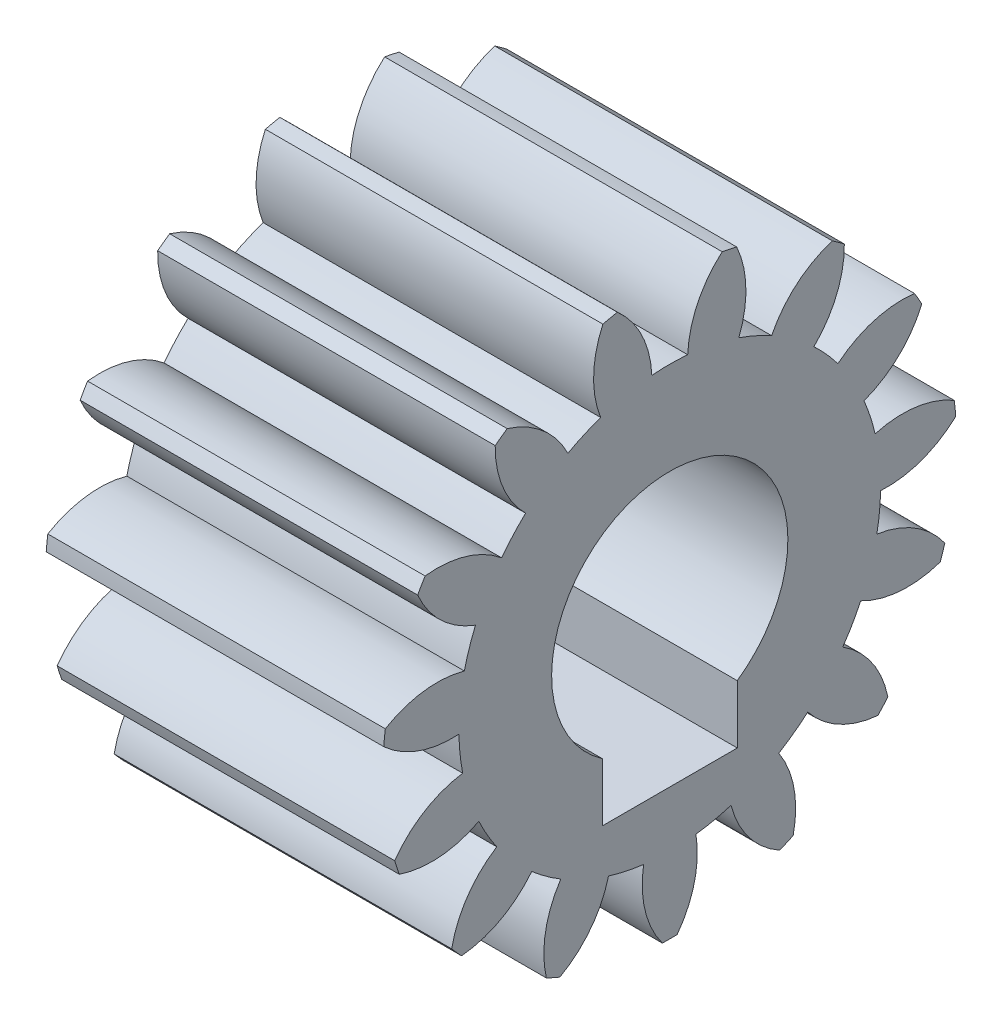
SolidWorks part; units mm, degrees
ref_plane "Plane1" through (0, 0, 0) normal (0, 0, 1) x (1, 0, 0)
ref_plane "Plane2" through (0, 0, 0) normal (0, 1, 0) x (1, 0, 0)
ref_plane "Plane3" through (0, 0, 0) normal (1, 0, 0) x (0, 0, -1)
sketch "HoldingSke" plane through (0, 0, 0) normal (0, 1, 0) x (1, 0, 0)
  line L0 (0, 0) -> (1.9319, -0.5176)
  line L1 (-15, 0) -> (100, 0) construction
  line L2 (0, 0) -> (-2.1039, 2.3779)
  line L3 (0, 0) -> (-11.863, 4.5341)
  line L4 (0, 0) -> (8.3417, 2.2352)
  line L5 (0, 0) -> (-46.8476, -17.4728)
  line L6 (0, 0) -> (-4.1448, -2.7965)
  line L7 (-2.1039, 2.3779) -> (8.6586, 51.2059)
  line L8 (-76.2, 54.61) -> (-76.1, 54.61)
  line L9 (-71.009, 38.7566) -> (-53.1078, 45.2721)
  line L10 (-76.2, 71.12) -> (104.1128, 71.12)
  line L11 (0, 0) -> (-5, 0)
  line L12 (-76.2, 101.6) -> (-76.181, 101.6)
  line L13 (24.9733, 27.94) -> (52.9518, 28.4284)
  line L14 (24.9733, 27.94) -> (24.9743, 27.94)
  line L15 (24.9733, 27.94) -> (100.4006, 29.5858)
  line L16 (-63.627, -0.5) -> (-12.827, -0.5)
  circle A0 centre (0, 0) radius 0.5
  circle A1 centre (0, 0) radius 3.124
  circle A2 centre (0, 0) radius 37.5
  circle A3 centre (0, 0) radius 0.5
  dimension "MHD" = 6.248
  dimension "Hub_dia" = 75
  dimension "Bore" = 1
  dimension "MBD" = 1
  dimension "Num_teeth" = 15
  dimension "Pitch" = 2
  dimension "Overall_len" = 50
  dimension "Show_teeth" = 15
  dimension "Thickness" = 5
  dimension "OAL" = 50.0001
  dimension "T_dim" = 0.1
  dimension "Ap" = 20
  dimension "H" = 19.05
  dimension "Pitch_radius" = 180.3128
  dimension "Width" = 5
  dimension "Backlash" = 0.019
  dimension "Addendum_fac" = 1
  dimension "Dedendum_fac" = 1.25
  dimension "Clearance_fac" = 0.25
  dimension "Dedendum_add" = 0.001
  dimension "Module" = 0.5
sketch "BasProSke" plane through (0, 0, 0) normal (0, 1, 0) x (1, 0, 0)
  line L0 (-10, 0) -> (60, 0) construction
  line L1 (0, 0) -> (0, 4.25)
  line L2 (0, 0) -> (5, 0)
  line L3 (5, 0) -> (5, 4.25)
  line L4 (5, 4.25) -> (0, 4.25)
  dimension "Thickness" = 5
  dimension "Diameter" = 8.5
revolve "Base-Revolve" add sketch "BasProSke" angle 360 about L0
sketch "TooCutSke" plane through (0, 0, 0) normal (1, 0, 0) x (0, 0, -1)
  line L1 (0, 0) -> (0, 107) construction
  line L2 (0, 0) -> (-0.4252, 3.7258) construction
  line L3 (0, 0) -> (-1.5522, 7.3025) construction
  line L4 (-0.4252, 3.7258) -> (-0.7761, 3.6512) construction
  arc A0 (0.2658, 3.1127) -> (-0.2658, 3.1127) centre (0, 0) ccw
  arc A1 (0.8008, 4.1997) -> (-0.8008, 4.1997) centre (0, 0) ccw
  circle A2 centre (0, 0) radius 3.75 construction
  circle A3 centre (0, 0) radius 3.5238 construction
  arc A4 (-0.2658, 3.1127) -> (-0.8008, 4.1997) centre (-1.7645, 3.0503) ccw
  arc A5 (0.8008, 4.1997) -> (0.2658, 3.1127) centre (1.7645, 3.0503) ccw
  dimension "Root_dia" = 6.248
  dimension "Overcut_dia" = 8.5508
  dimension "Pitch_dia" = 7.5
  dimension "Base_dia" = 7.0477
  dimension "Flank_rad" = 1.5
  dimension "Half_ang" = 12
  dimension "Half_CT" = 0.3587
extrude "ToothCut" cut sketch "TooCutSke" along normal through all
fillet "Breaks" [suppressed] radius 0.01
fillet "RootFillets" [suppressed] radius 0.126
pattern_circular "TeethCuts" count 15 every 24 about axis through (-10, 0, 0) along (1, 0, 0) of "ToothCut", "RootFillets", "Breaks"
sketch "HubNeaOneSke" plane through (0, 0, 0) normal (-1, 0, 0) x (0, 0, 1)
  circle A0 centre (0, 0) radius 3.124
  dimension "Diameter" = 6.248
extrude "HubNearOne" [suppressed] add sketch "HubNeaOneSke" along normal blind 45.0001
sketch "HubNeaBotSke" plane through (0, 0, 0) normal (-1, 0, 0) x (0, 0, 1)
  circle A0 centre (0, 0) radius 3.124
  dimension "Diameter" = 6.248
extrude "HubNearBoth" [suppressed] add sketch "HubNeaBotSke" along normal blind 22.5
ref_plane "FarPln" through (5, 0, 0) normal (1, 0, 0) x (0, 0, -1)
sketch "HubFarSke" plane through (5, 0, 0) normal (1, 0, 0) x (0, 0, -1)
  circle A0 centre (0, 0) radius 3.124
  dimension "Diameter" = 6.248
extrude "HubFar" [suppressed] add sketch "HubFarSke" along normal blind 22.5
sketch "BorSke" plane through (0, 0, 0) normal (1, 0, 0) x (0, 0, -1)
  circle A0 centre (0, 0) radius 0.5
  dimension "Diameter" = 1
extrude "Bore" cut sketch "BorSke" along normal mid plane 100.0001
sketch "KeySke" plane through (0, 0, 0) normal (1, 0, 0) x (0, 0, -1)
  line L0 (-0.05, 0) -> (-0.05, 0.6)
  line L1 (-0.05, 0.6) -> (0.05, 0.6)
  line L2 (0.05, 0.6) -> (0.05, 0)
  line L3 (0, 0) -> (0, 34) construction
  line L4 (-0.05, 0) -> (0.05, 0)
  dimension "Offset" = 0.6
  dimension "Width" = 0.1
extrude "Keyway" [suppressed] cut sketch "KeySke" along normal mid plane 100.0001
pattern_circular "Keyway2" [suppressed] count 2 every 90 about axis through (-10, 0, 0) along (1, 0, 0)
sketch "Sketch1" plane through (5, 0, 0) normal (1, 0, 0) x (0, 0, -1)
  circle A0 centre (0, 0) radius 1.75
  dimension "D1" = 3.5
extrude "Cut-Extrude1" cut sketch "Sketch1" against normal through all both and the other way through all
sketch "Sketch2" plane through (5, 0, 0) normal (1, 0, 0) x (0, 0, -1)
  line L0 (0, 0) -> (0, -3.7965) construction
  line L1 (-1, -1.2) -> (1, -1.2)
  line L2 (-1, -1.2) -> (-1, -2.3)
  line L3 (-1, -2.3) -> (1, -2.3)
  line L4 (1, -1.2) -> (1, -2.3)
  line L5 (0, -2.3) -> (0, -1.2) construction
  line L6 (-1, -1.75) -> (1, -1.75) construction
  circle A0 centre (0, 0) radius 1.75 construction
  point P0 (0, -1.75)
  dimension "D1" = 2.3
  dimension "D2" = 2
extrude "Cut-Extrude2" cut sketch "Sketch2" against normal through all both and the other way through all
equation "' \"Module@HoldingSke\" = 6.35"
equation "' \"Num_teeth@HoldingSke\" = 12"
equation "' \"Ap@HoldingSke\" =  20"
equation "' \"Ap@HoldingSke\" = 20"
equation "' \"Width@HoldingSke\" = 0.5 * 25.4"
equation "' \"Hub_dia@HoldingSke\"= 1 * 25.4"
equation "' \"Hub_dia@HoldingSke\" = 1 * 25.4"
equation "' \"Overall_len@HoldingSke\" = 1.0 * 25.4"
equation "' \"Bore@HoldingSke\" = 0.75 * 25.4"
equation "' \"T_dim@HoldingSke\" = 0.1 * 25.4"
equation "' \"Width@KeySke\" = 0.25 * 25.4"
equation "' \"Show_teeth@HoldingSke\" = 13"
equation "' \"Backlash@HoldingSke\" = 0.009 * 25.4"
equation "' \"Addendum_fac@HoldingSke\" = 1.0"
equation "' \"Dedendum_fac@HoldingSke\" = 1.25"
equation "' \"Dedendum_add@HoldingSke\" = 0.00005 * 25.4"
equation "' \"Clearance_fac@HoldingSke\" = 0.25"
equation "\"Pitch@HoldingSke\" = 1 / \"Module@HoldingSke\""
equation "\"Overcut_dia@TooCutSke\" = (\"Num_teeth@HoldingSke\" + 2 * \"Addendum_fac@HoldingSke\") / \"Pitch@HoldingSke\" + 0.002 * 25.4"
equation "\"Pitch_dia@TooCutSke\" = \"Num_teeth@HoldingSke\" / \"Pitch@HoldingSke\""
equation "\"Base_dia@TooCutSke\" = \"Num_teeth@HoldingSke\" / \"Pitch@HoldingSke\" * cos((\"Ap@HoldingSke\"  * 3.14159265 / 180))"
equation "\"Root_dia@TooCutSke\" = (\"Num_teeth@HoldingSke\" + 2) / \"Pitch@HoldingSke\" - 2 * (\"Addendum_fac@HoldingSke\" + \"Dedendum_fac@HoldingSke\") / \"Pitch@HoldingSke\" - \"Dedendum_add@HoldingSke\" * 2"
equation "\"Half_ang@TooCutSke\" = 180 / \"Num_teeth@HoldingSke\""
equation "\"Half_CT@TooCutSke\" = \"Num_teeth@HoldingSke\" / \"Pitch@HoldingSke\" * sin((3.14159265 / 2 / \"Num_teeth@HoldingSke\")) / 2 - 7 * \"Backlash@HoldingSke\" / 4"
equation "\"Flank_rad@TooCutSke\" = \"Num_teeth@HoldingSke\" / \"Pitch@HoldingSke\" / 5"
equation "\"Radius@RootFillets\" = \"Clearance_fac@HoldingSke\" / \"Pitch@HoldingSke\" + \"Dedendum_add@HoldingSke\""
equation "\"Break_rad@Breaks\" = 0.02 / \"Pitch@HoldingSke\""
equation "\"Thickness@HoldingSke\" = \"Width@HoldingSke\""
equation "\"OAL@HoldingSke\" = \"Thickness@HoldingSke\""
equation "\"MHD@HoldingSke\" = (\"Num_teeth@HoldingSke\" + 2) / \"Pitch@HoldingSke\" - 2 * (\"Addendum_fac@HoldingSke\" + \"Dedendum_fac@HoldingSke\")  / \"Pitch@HoldingSke\" - \"Dedendum_add@HoldingSke\" * 2"
equation "\"MBD@HoldingSke\" = (\"Num_teeth@HoldingSke\" + 2) / \"Pitch@HoldingSke\" - 2 * (\"Addendum_fac@HoldingSke\" + \"Dedendum_fac@HoldingSke\")  / \"Pitch@HoldingSke\" - \"Dedendum_add@HoldingSke\" * 2 - 0.002 * 25.4"
equation "\"MHD@HoldingSke\" = ((sgn( \"MHD@HoldingSke\" - \"Hub_dia@HoldingSke\" )-1)*( \"MHD@HoldingSke\" - \"Hub_dia@HoldingSke\" ))/-2+ \"Hub_dia@HoldingSke\""
equation "\"MBD@HoldingSke\" = ((sgn( \"MBD@HoldingSke\" - \"Bore@HoldingSke\" )-1)*( \"MBD@HoldingSke\" - \"Bore@HoldingSke\" ))/-2+ \"Bore@HoldingSke\""
equation "\"OAL@HoldingSke\" = ((sgn( \"OAL@HoldingSke\" - \"Overall_len@HoldingSke\" )+1)*( \"OAL@HoldingSke\" - \"Overall_len@HoldingSke\" ))/2 + \"Overall_len@HoldingSke\" + 0.000002 * 25.4"
equation "\"Num_teeth@TeethCuts\" = int( \"Show_teeth@HoldingSke\" ) + 1"
equation "\"Num_teeth@TeethCuts\" = ((sgn( \"Num_teeth@TeethCuts\" - \"Num_teeth@HoldingSke\" )-1)*( \"Num_teeth@TeethCuts\" - \"Num_teeth@HoldingSke\" ))/-2+ \"Num_teeth@HoldingSke\""
equation "\"Num_teeth@TeethCuts\" = ((sgn( \"Num_teeth@TeethCuts\" - 2.0)+1)*( \"Num_teeth@TeethCuts\" - 2.0))/2 +2.0"
equation "\"Angle@TeethCuts\" = 360.0 / \"Num_teeth@HoldingSke\""
equation "\"Diameter@BasProSke\" = (\"Num_teeth@HoldingSke\" + 2 * \"Addendum_fac@HoldingSke\") / \"Pitch@HoldingSke\""
equation "\"Thickness@BasProSke\"  = \"Thickness@HoldingSke\""
equation "' \"Fillet_rad@BasProSke\" =  \"Thickness@HoldingSke\" * 0.05"
equation "' \"Fillet_rad@BasProSke\" = \"Thickness@HoldingSke\" * 0.05"
equation "\"MHD@HoldingSke\" = ((sgn( \"MHD@HoldingSke\" - \"Root_dia@TooCutSke\" )-1)*( \"MHD@HoldingSke\" - \"Root_dia@TooCutSke\" ))/-2+ \"Root_dia@TooCutSke\""
equation "\"Diameter@HubNeaOneSke\" = \"MHD@HoldingSke\""
equation "\"Length@HubNearOne\" = \"OAL@HoldingSke\" - \"Thickness@BasProSke\""
equation "\"Diameter@HubNeaBotSke\" = \"MHD@HoldingSke\""
equation "\"Length@HubNearBoth\" = ( \"OAL@HoldingSke\" - \"Thickness@BasProSke\" ) / 2.0"
equation "\"Thickness@FarPln\" = \"Thickness@BasProSke\""
equation "\"Diameter@HubFarSke\" = \"MHD@HoldingSke\""
equation "\"Length@HubFar\" = ( \"OAL@HoldingSke\" - \"Thickness@BasProSke\" ) / 2.0"
equation "\"Diameter@BorSke\" = \"MBD@HoldingSke\""
equation "\"D1@Bore\" = \"OAL@HoldingSke\" * 2.0"
equation "\"D1@Keyway\" = \"OAL@HoldingSke\" * 2.0"
equation "\"Offset@KeySke\" = \"T_dim@HoldingSke\" + \"MBD@HoldingSke\" / 2.0"
